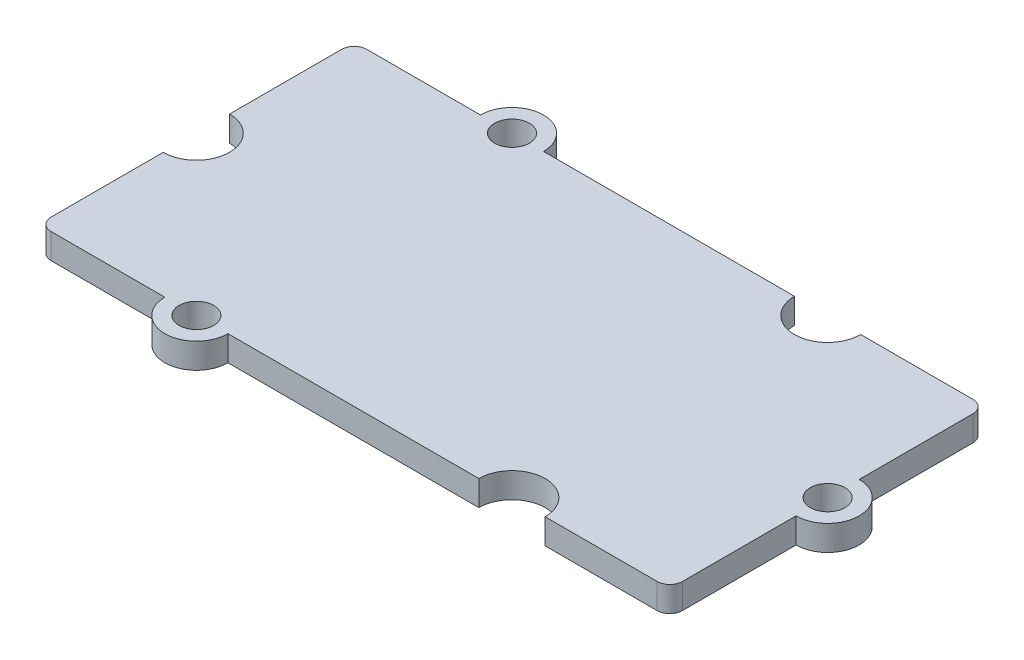
SolidWorks part; units mm, degrees
ref_plane "Plan de face" through (0, 0, 0) normal (0, 0, 1) x (1, 0, 0)
ref_plane "Plan de dessus" through (0, 0, 0) normal (0, 1, 0) x (1, 0, 0)
ref_plane "Plan de droite" through (0, 0, 0) normal (1, 0, 0) x (0, 0, -1)
sketch "Esquisse1" plane through (0, 0, 0) normal (0, 1, 0) x (1, 0, 0)
  line L1 (-19.2, -10) -> (19.2, -10)
  line L2 (-20, -9.2) -> (-20, 9.2)
  line L3 (-19.2, 10) -> (19.2, 10)
  line L4 (20, -9.2) -> (20, 9.2)
  line L5 (-20, -10) -> (20, 10) construction
  line L6 (-20, 10) -> (20, -10) construction
  circle A0 centre (-10, 10) radius 2
  circle A1 centre (-10, -10) radius 2
  circle A2 centre (-20, 0) radius 2.1
  circle A3 centre (10, 10) radius 2.1
  circle A4 centre (-10, 10) radius 1.1
  arc A5 (19.2, 10) -> (20, 9.2) centre (19.2, 9.2) cw
  circle A6 centre (-10, -10) radius 1.1
  arc A7 (-19.2, -10) -> (-20, -9.2) centre (-19.2, -9.2) cw
  arc A8 (19.2, -10) -> (20, -9.2) centre (19.2, -9.2) ccw
  arc A9 (-20, 9.2) -> (-19.2, 10) centre (-19.2, 9.2) cw
  circle A10 centre (10, -10) radius 2.1
  circle A11 centre (20, 0) radius 2
  circle A12 centre (20, 0) radius 1.1
  point P0 (0, 0)
  dimension "D2" = 0.8
  dimension "D3" = 4.2
  dimension "D4" = 2.2
  dimension "D5" = 4
  dimension "D7" = 10
  dimension "D8" = 30
  dimension "D1" = 40
  dimension "D6" = 20
extrude "Boss.-Extru.1" add sketch "Esquisse1" along normal mid plane 1.6 contours A9 L2 A2 A7 L1 A1 A8 L4 A3 A5 L3 A0 | A4 L3 A0 | A4 L3 A0 | A6 L1 A1 | A6 L1 A1 | A12 L4 A11 | A12 L4 A11
